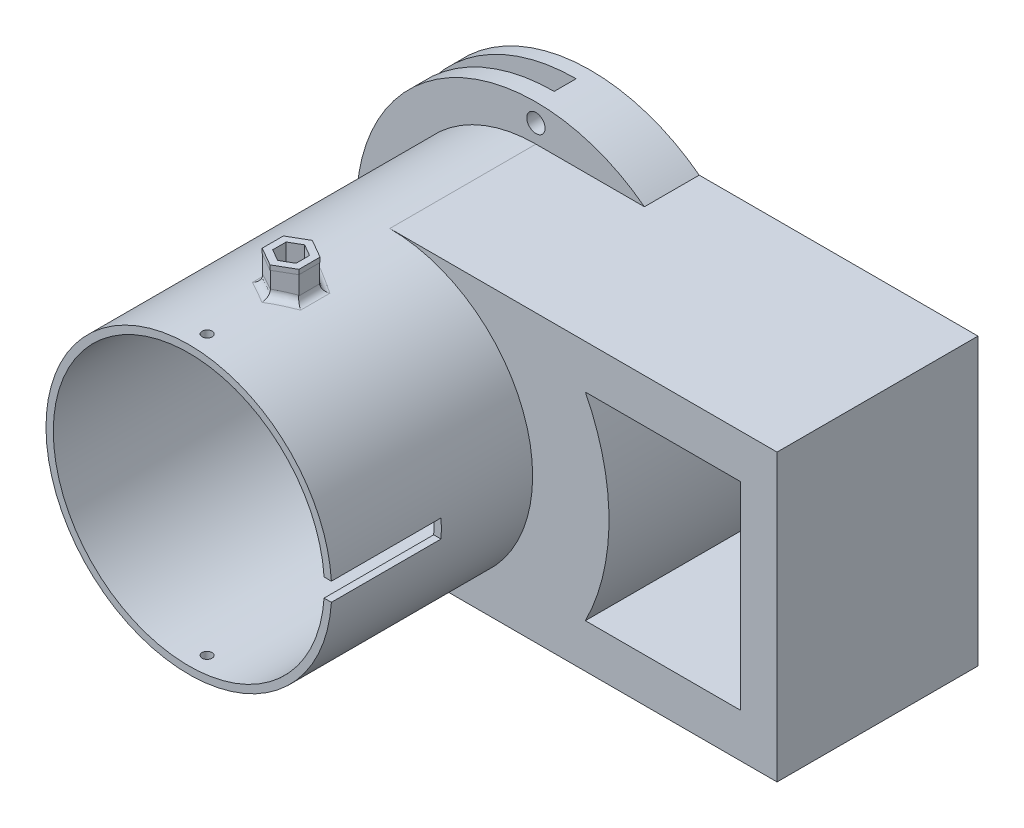
SolidWorks part; units mm, degrees
material "ABS"
ref_plane "Front Plane" through (0, 0, 0) normal (0, 0, 1) x (1, 0, 0)
ref_plane "Top Plane" through (0, 0, 0) normal (0, 1, 0) x (1, 0, 0)
ref_plane "Right Plane" through (0, 0, 0) normal (1, 0, 0) x (0, 0, -1)
sketch "Sketch1" plane through (0, 0, 0) normal (0, 0, 1) x (1, 0, 0)
  circle A0 centre (0, 0) radius 49.657
  circle A1 centre (0, 0) radius 47.117
  dimension "D1" = 2.54
  dimension "D2" = 94.234
extrude "Boss-Extrude1" add sketch "Sketch1" along normal mid plane 139.7
sketch "Sketch2" plane through (0, 0, -69.85) normal (0, 0, -1) x (-1, 0, 0)
  circle A1 centre (0, 0) radius 49.657 construction
  circle A2 centre (0, 0) radius 49.657
  circle A4 centre (0, 0) radius 62.357
  dimension "D1" = 12.7
extrude "Boss-Extrude2" add sketch "Sketch2" against normal blind 19.05
hole_wizard "#8-32 Tapped Hole1" positions "Sketch4" profile "Sketch5" tap size "#8-32" standard "ANSI Inch"
sketch "Sketch4" plane through (0, 0, 0) normal (0, 1, 0) x (1, 0, 0)
  line L0 (-49.657, -69.85) -> (49.657, -69.85) construction
  point P0 (0, -63.5)
  dimension "D1" = 6.35
sketch "Sketch5" plane through (0, 0, 63.5) normal (1, 0, 0) x (0, 0, -1)
  line L0 (0, 0) -> (0, 62.357)
  line L1 (0, 62.357) -> (1.7272, 62.357)
  line L2 (1.7272, 62.357) -> (1.7272, 0.9906)
  line L3 (1.7272, 0.9906) -> (2.7178, 0)
  line L5 (2.7178, 0) -> (0, 0)
  line L6 (-1.7272, 0.9906) -> (-2.7178, 0) construction
  line L11 (0, -6.35) -> (0, 107.95) construction
  dimension "Thru Tap Drill Dia." = 3.4544
  dimension "Thru Tap Drill Depth" = 62.357
  dimension "Near C'Sink Dia." = 5.4356
  dimension "Near C'Sink Angle" = 90
cosmetic thread "Hole Thread1" parameters "D1"=3.048, "D2"=4.1656
mirror "Mirror1" about plane through (0, 0, 0) normal (0, 1, 0) of "#8-32 Tapped Hole1"
sketch "Sketch6" plane through (0, 0, 0) normal (0, 0, 1) x (1, 0, 0)
  circle A4 centre (0, 0) radius 56.007
  circle A5 centre (0, 0) radius 56.007
  dimension "D1" = 6.35
hole_wizard "1/4 (0.2500) Dowel Hole1" positions "Sketch8" profile "Sketch9" hole size "1/4" standard "ANSI Inch" end condition through all
sketch "Sketch8" plane through (0, 0, -50.8) normal (0, 0, 1) x (1, 0, 0)
  circle A0 centre (0, 0) radius 56.007 construction
  point P0 (-56.007, 0)
  point P4 (0, 56.007)
  point P6 (56.007, 0)
  point P8 (0, -56.007)
sketch "Sketch9" plane through (-56.007, 0, -50.8) normal (1, 0, 0) x (0, -1, 0)
  line L0 (0, 0) -> (0, 19.05)
  line L1 (0, 19.05) -> (3.175, 19.05)
  line L2 (3.175, 19.05) -> (3.175, 0)
  line L5 (3.175, 0) -> (0, 0)
  line L11 (0, -6.35) -> (0, 107.95) construction
  dimension "Thru Hole Dia." = 6.35
  dimension "Thru Hole Depth" = 19.05
sketch "Sketch10" plane through (0, 0, 0) normal (1, 0, 0) x (0, 0, -1)
  line L0 (-69.85, 49.657) -> (-69.85, -49.657) construction
  line L1 (-69.85, 3.175) -> (-31.75, 3.175)
  line L2 (-69.85, 3.175) -> (-69.85, -3.175)
  line L3 (-69.85, -3.175) -> (-31.75, -3.175)
  line L4 (-31.75, 3.175) -> (-31.75, -3.175)
  point P12 (-69.85, 0)
  dimension "D1" = 6.35
  dimension "D2" = 38.1
extrude "Cut-Extrude1" cut sketch "Sketch10" along normal through all
sketch "Sketch12" plane through (0, 0, 0) normal (1, 0, 0) x (0, 0, -1)
  circle A0 centre (0, 0) radius 3.175
  dimension "D1" = 6.35
extrude "Cut-Extrude3" cut sketch "Sketch12" against normal through all
sketch "Sketch14" plane through (0, 0, 0) normal (1, 0, 0) x (0, 0, -1)
  circle A1 centre (0, 0) radius 3.429
  circle A2 centre (0, 0) radius 3.175
  circle A3 centre (0, 0) radius 3.175 construction
  dimension "D1" = 0.254
extrude "Cut-Extrude4" cut sketch "Sketch14" against normal up to next
sketch "Sketch15" plane through (0, 0, 0) normal (0, 1, 0) x (1, 0, 0)
  line L0 (-49.657, -69.85) -> (49.5554, -69.85) construction
  circle A0 centre (0, -34.29) radius 1.905
  dimension "D1" = 3.81
  dimension "D2" = 35.56
extrude "Cut-Extrude5" cut sketch "Sketch15" along normal up to next
sketch "Sketch16" plane through (0, 0, 0) normal (0, 1, 0) x (1, 0, 0)
  line L1 (0, -41.5227) -> (6.2637, -37.9064)
  line L2 (6.2637, -37.9064) -> (6.2637, -30.6736)
  line L3 (6.2637, -30.6736) -> (0, -27.0573)
  line L4 (0, -27.0573) -> (-6.2637, -30.6736)
  line L5 (-6.2637, -30.6736) -> (-6.2637, -37.9064)
  line L6 (-6.2637, -37.9064) -> (0, -41.5227)
  line L7 (-4.064, -31.9436) -> (-4.064, -36.6364)
  line L8 (-4.064, -36.6364) -> (0, -38.9827)
  line L9 (0, -38.9827) -> (4.064, -36.6364)
  line L10 (4.064, -36.6364) -> (4.064, -31.9436)
  line L11 (4.064, -31.9436) -> (0, -29.5973)
  line L12 (0, -29.5973) -> (-4.064, -31.9436)
  circle A0 centre (0, -34.29) radius 1.905
  circle A1 centre (0, -34.29) radius 1.905 construction
  circle A2 centre (0, -34.29) radius 6.2637 construction
  circle A3 centre (0, -34.29) radius 4.064 construction
  dimension "D1" = 2.54
  dimension "D2" = 8.128
  dimension "D3" = 0
extrude "Boss-Extrude4" add sketch "Sketch16" along normal blind 8.89 from offset 49.022 contours L5 L6 L1 L2 L3 L4 L12 L11 L10 L9 L8 L7
fillet "Fillet3" radius 2.54 6 edges at (-3.1381, 49.5577, 28.8691) (-6.2637, 49.2604, 34.29) (3.1381, 49.5577, 28.8691) (6.2637, 49.2604, 34.29) (-3.1381, 49.5577, 39.7109) (3.1381, 49.5577, 39.7109)
sketch "Sketch17" plane through (0, 57.912, 0) normal (0, 1, 0) x (1, 0, 0)
  line L0 (4.064, -36.6364) -> (4.064, -31.9436) construction
  line L1 (-4.064, -36.6364) -> (0, -38.9827)
  line L2 (0, -38.9827) -> (4.064, -36.6364)
  line L3 (4.064, -36.6364) -> (4.064, -31.9436)
  line L4 (4.064, -31.9436) -> (0, -29.5973)
  line L5 (0, -29.5973) -> (-4.064, -31.9436)
  line L6 (-4.064, -31.9436) -> (-4.064, -36.6364)
  line L7 (-6.3747, -37.9704) -> (0, -41.6509)
  line L8 (0, -41.6509) -> (6.3747, -37.9704)
  line L9 (6.3747, -37.9704) -> (6.3747, -30.6096)
  line L10 (6.3747, -30.6096) -> (0, -26.9291)
  line L11 (0, -26.9291) -> (-6.3747, -30.6096)
  line L12 (-6.3747, -30.6096) -> (-6.3747, -37.9704)
  circle A0 centre (0, -34.29) radius 4.064 construction
  circle A1 centre (0, -34.29) radius 6.3747 construction
extrude "Boss-Extrude5" add sketch "Sketch17" along normal blind 1.6256
sketch "Sketch18" plane through (0, 0, 0) normal (0, 0, 1) x (1, 0, 0)
  line L0 (0, 0) -> (0, 55.0468) construction
  line L3 (0, 57.912) -> (0, 52.1815) construction
  line L4 (134.62, -47.117) -> (0, -47.117)
  line L5 (0, 47.117) -> (134.62, 47.117)
  line L6 (0, 47.117) -> (0, 49.657)
  line L7 (0, 49.657) -> (134.62, 49.657)
  line L8 (134.62, 47.117) -> (134.62, 49.657)
  line L9 (134.62, -47.117) -> (134.62, -49.657)
  line L10 (134.62, -49.657) -> (0, -49.657)
  line L11 (0, -47.117) -> (0, -49.657)
  line L12 (0, 0) -> (0, -56.007) construction
  circle A2 centre (0, 0) radius 47.117 construction
  dimension "D3" = 134.62
  dimension "D4" = 2.54
extrude "Boss-Extrude6" add sketch "Sketch18" against normal through all
sketch "Sketch20" plane through (0, 0, -69.85) normal (0, 0, -1) x (-1, 0, 0)
  circle A0 centre (0, 0) radius 59.5376
extrude "Cut-Extrude6" cut sketch "Sketch20" against normal blind 7.62 from offset 5.08 offset against normal yes
sketch "Sketch21" plane through (0, 0, 0) normal (1, 0, 0) x (0, 0, -1)
  line L0 (69.85, -62.357) -> (69.85, 62.357) construction
  line L1 (64.77, 62.357) -> (57.15, 62.357)
  line L2 (64.77, 62.357) -> (64.77, -62.611)
  line L3 (64.77, -62.611) -> (57.15, -62.611)
  line L4 (57.15, 62.357) -> (57.15, -62.611)
  line L5 (69.85, 62.357) -> (50.8, 62.357) construction
  dimension "D1" = 7.62
  dimension "D2" = 5.08
  dimension "D3" = 124.968
extrude "Cut-Extrude7" cut sketch "Sketch21" against normal up to next
sketch "Sketch22" plane through (0, 0, -50.8) normal (0, 0, 1) x (1, 0, 0)
  line L0 (0, 49.657) -> (37.7171, 49.657)
  line L1 (134.62, 49.657) -> (0, 49.657) construction
  line L2 (0, -49.657) -> (37.7171, -49.657)
  line L3 (0, -49.657) -> (134.62, -49.657) construction
  line L4 (37.7171, -49.657) -> (0, -49.657) construction
  arc A0 (0, -49.657) -> (0, 49.657) centre (0, 0) ccw
  arc A1 (8.3753, 48.9456) -> (0, 49.657) centre (0, 0) ccw construction
  arc A2 (37.7171, 49.657) -> (37.7171, -49.657) centre (0, 0) cw
  arc A3 (40.8459, -47.117) -> (40.8459, 47.117) centre (0, 0) ccw construction
extrude "Boss-Extrude7" add sketch "Sketch22" along normal up to surface (50.8 mm away) up to face at (71.2551, 48.5447, 0)
sketch "Sketch23" plane through (0, 0, 0) normal (0, 0, 1) x (1, 0, 0)
  line L0 (40.8459, 47.117) -> (134.62, 47.117)
  line L1 (134.62, 47.117) -> (134.62, -47.117)
  line L2 (134.62, -47.117) -> (40.8459, -47.117)
  line L3 (67.9846, 34.417) -> (121.92, 34.417)
  line L4 (121.92, 34.417) -> (121.92, -34.417)
  line L5 (121.92, -34.417) -> (67.9846, -34.417)
  arc A0 (40.8459, 47.117) -> (40.8459, -47.117) centre (0, 0) cw
  arc A1 (40.8459, -47.117) -> (40.8459, 47.117) centre (0, 0) ccw construction
  arc A2 (67.9846, 34.417) -> (67.9846, -34.417) centre (0, 0) cw
  point P14 (76.2, 0)
  dimension "D1" = 76.2
  dimension "D2" = 12.7
  dimension "D3" = 12.7
  dimension "D4" = 12.7
extrude "Boss-Extrude8" add sketch "Sketch23" against normal through all
